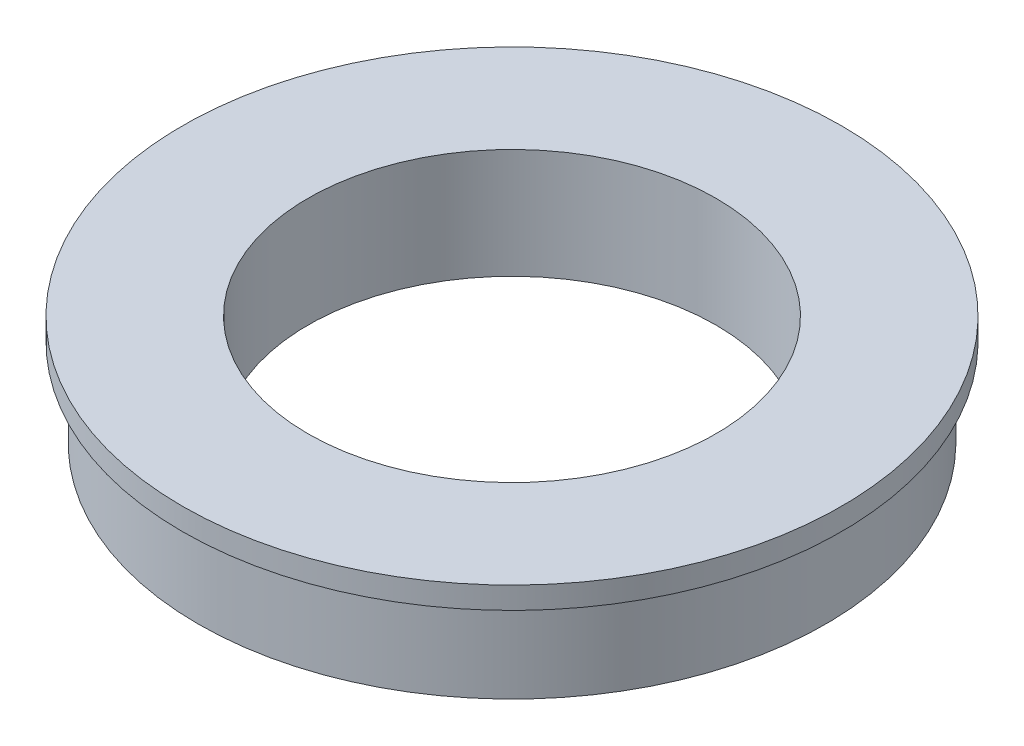
SolidWorks part; units mm, degrees
ref_plane "Plan de face" through (0, 0, 0) normal (0, 0, 1) x (1, 0, 0)
ref_plane "Plan de dessus" through (0, 0, 0) normal (0, 1, 0) x (1, 0, 0)
ref_plane "Plan de droite" through (0, 0, 0) normal (1, 0, 0) x (0, 0, -1)
sketch "Esquisse1" plane through (0, 0, 0) normal (0, 1, 0) x (1, 0, 0)
  circle A0 centre (0, 0) radius 10
  circle A1 centre (0, 0) radius 6.5
  dimension "D1" = 13
  dimension "D2" = 20
extrude "Extrusion1" add sketch "Esquisse1" against normal blind 3.5
sketch "Esquisse2" plane through (0, 0, 0) normal (0, 1, 0) x (-1, 0, 0)
  circle A0 centre (0, 0) radius 10
  circle A1 centre (0, 0) radius 10.5
  circle A2 centre (0, 0) radius 10 construction
  dimension "D1" = 21
extrude "Extrusion2" add sketch "Esquisse2" against normal blind 0.7
shell "Coque1" thickness 1
